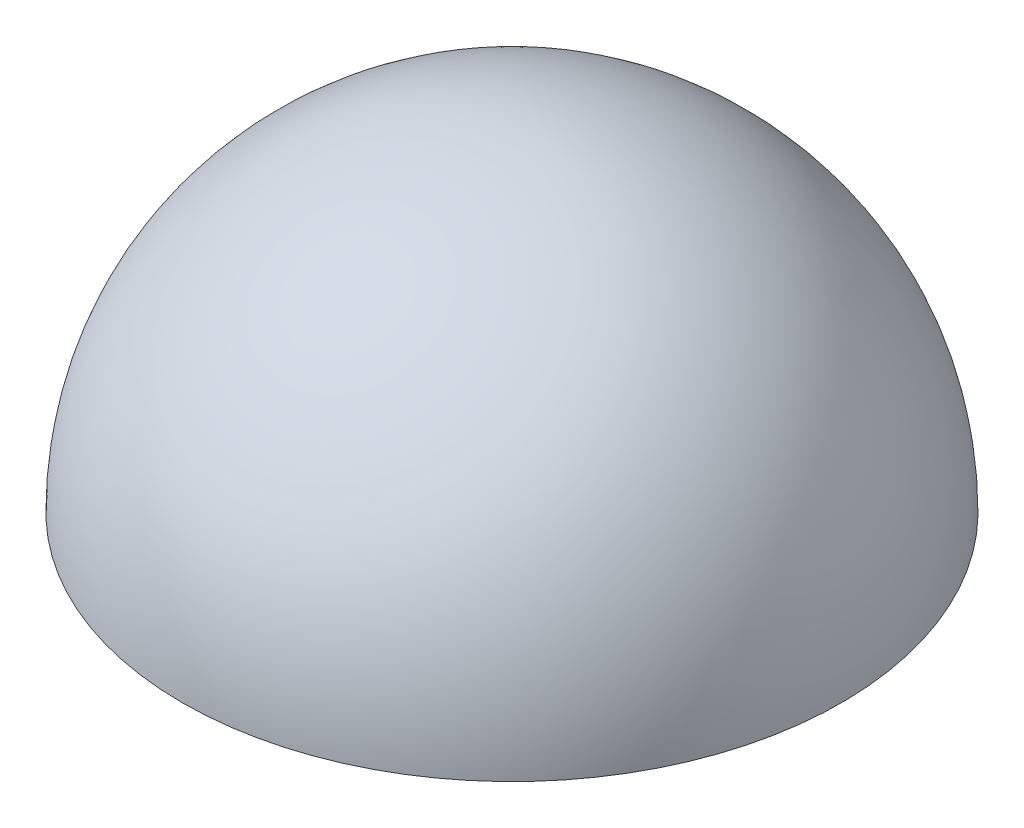
SolidWorks part; units mm, degrees
other "Markup1"
sketch "Sketch2"
ref_plane "Front Plane" through (0, 0, 0) normal (0, 0, 1) x (1, 0, 0)
ref_plane "Top Plane" through (0, 0, 0) normal (0, 1, 0) x (1, 0, 0)
ref_plane "Right Plane" through (0, 0, 0) normal (1, 0, 0) x (0, 0, -1)
sketch "Sketch1" plane through (0, 0, 0) normal (0, 1, 0) x (1, 0, 0)
  line L0 (0, 0) -> (0, 50)
  arc A2 (0, 0) -> (0, 50) centre (0, 25) ccw
revolve "Revolve3" add sketch "Sketch1" angle 180 about L0
